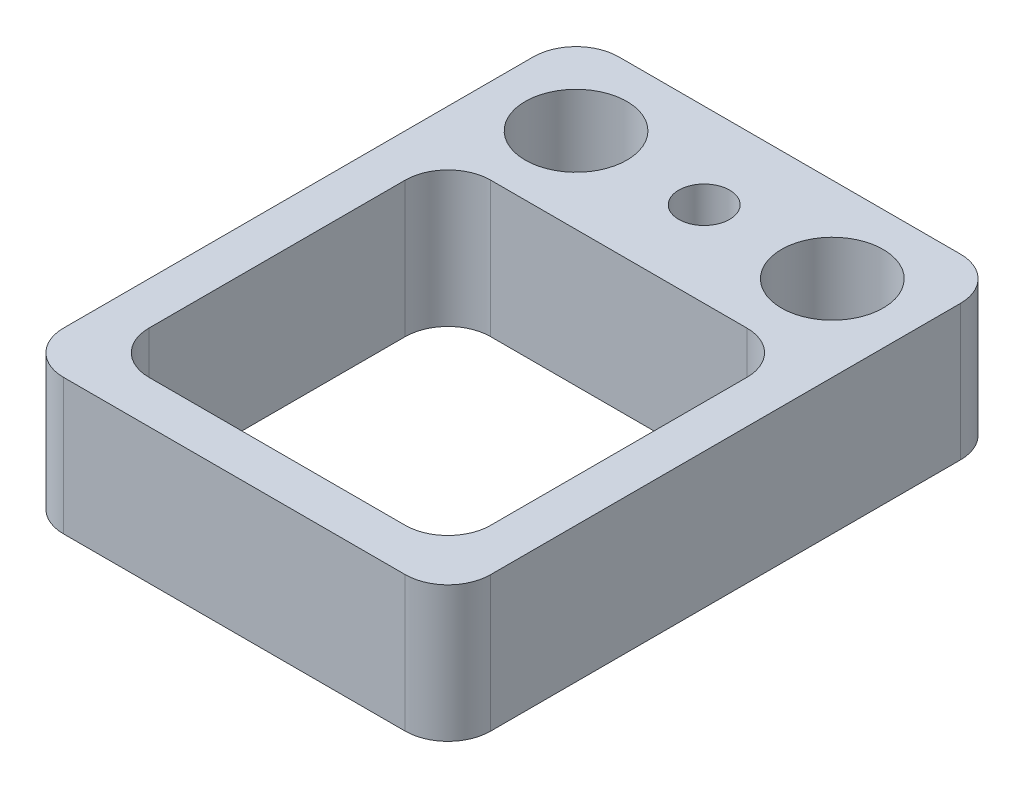
SolidWorks part; units mm, degrees
ref_plane "Front Plane" through (0, 0, 0) normal (0, 0, 1) x (1, 0, 0)
ref_plane "Top Plane" through (0, 0, 0) normal (0, 1, 0) x (1, 0, 0)
ref_plane "Right Plane" through (0, 0, 0) normal (1, 0, 0) x (0, 0, -1)
sketch "Sketch1" plane through (0, 0, 0) normal (0, 1, 0) x (1, 0, 0)
  line L1 (5, -6.5) -> (-5, -6.5)
  line L2 (5, -6.5) -> (5, 6.5)
  line L3 (5, 6.5) -> (-5, 6.5)
  line L4 (-5, -6.5) -> (-5, 6.5)
  line L5 (5, -6.5) -> (-5, 6.5) construction
  line L6 (5, 6.5) -> (-5, -6.5) construction
  point P0 (0, 0)
  dimension "D1" = 10
  dimension "D2" = 13
extrude "Extrude1" add sketch "Sketch1" along normal blind 3.175
sketch "Sketch2" plane through (0, 3.175, 0) normal (0, 1, 0) x (1, 0, 0)
  line L0 (-5, 6.5) -> (-5, -6.5) construction
  line L1 (-4, -5.5) -> (4, -5.5)
  line L2 (-4, -5.5) -> (-4, 2.5)
  line L3 (-4, 2.5) -> (4, 2.5)
  line L4 (4, -5.5) -> (4, 2.5)
  line L5 (-5, -6.5) -> (5, -6.5) construction
  dimension "D1" = 8
  dimension "D2" = 8
  dimension "D3" = 1
  dimension "D4" = 1
extrude "Extrude2" cut sketch "Sketch2" against normal blind 3.5
hole_wizard "#0-80 Tapped Hole1" positions "3DSketch5" profile "Sketch9" tap size "#0-80" standard "Ansi Inch"
sketch3d "3DSketch5"
  line L0 (5, 3.175, -6.5) -> (-5, 3.175, -6.5) construction
  line L1 (5, 3.175, 6.5) -> (5, 3.175, -6.5) construction
  point P0 (0, 3.175, -4.5)
  dimension "D1" = 2
  dimension "D2" = 5
sketch "Sketch9" plane through (0, 3.175, -4.5) normal (1, 0, 0) x (0, 0, 1)
  line L0 (0, 0) -> (0, 4.3579)
  line L1 (0, 4.3579) -> (0.5956, 4)
  line L2 (0.5956, 4) -> (0.5956, 0)
  line L5 (0.5956, 0) -> (0, 0)
  line L10 (0, 4.3579) -> (-0.5956, 4) construction
  line L11 (0, -6.35) -> (0, 107.95) construction
  dimension "Tap Drill Dia." = 1.1913
  dimension "Tap Drill Depth" = 4
  dimension "Drill Angle" = 118
hole_wizard "3/32 (0.09375) Diameter Hole1" positions "3DSketch6" profile "Sketch10" hole size "3/32" standard "Ansi Inch"
sketch3d "3DSketch6"
  line L0 (5, 3.175, -6.5) -> (-5, 3.175, -6.5) construction
  line L1 (5, 3.175, 6.5) -> (5, 3.175, -6.5) construction
  line L2 (-5, 3.175, -6.5) -> (-5, 3.175, 6.5) construction
  point P0 (-3, 3.175, -4.5)
  point P2 (3, 3.175, -4.5)
  dimension "D1" = 2
  dimension "D2" = 2
  dimension "D3" = 2
  dimension "D4" = 2
sketch "Sketch10" plane through (-3, 3.175, -4.5) normal (1, 0, 0) x (0, 0, 1)
  line L0 (0, 0) -> (0, 10.7154)
  line L1 (0, 10.7154) -> (1.1906, 10)
  line L2 (1.1906, 10) -> (1.1906, 0)
  line L5 (1.1906, 0) -> (0, 0)
  line L10 (0, 10.7154) -> (-1.1906, 10) construction
  line L11 (0, -6.35) -> (0, 107.95) construction
  dimension "Hole Dia." = 2.3812
  dimension "Hole Depth" = 10
  dimension "Drill Angle" = 118
fillet "Fillet7" radius 1 8 edges at (-4, 1.5875, 5.5) (4, 1.5875, 5.5) (4, 1.5875, -2.5) (-4, 1.5875, -2.5) (-5, 1.5875, 6.5) (5, 1.5875, 6.5) (5, 1.5875, -6.5) (-5, 1.5875, -6.5)
